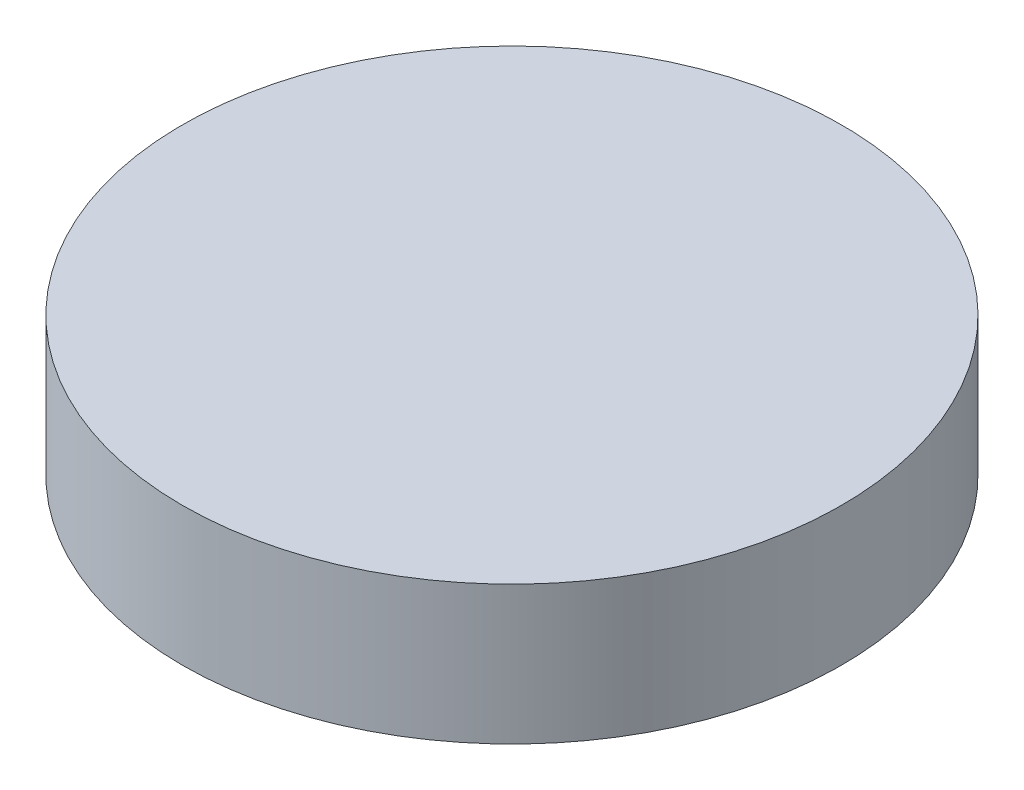
SolidWorks part; units mm, degrees
ref_plane "Front Plane" through (0, 0, 0) normal (0, 0, 1) x (1, 0, 0)
ref_plane "Top Plane" through (0, 0, 0) normal (0, 1, 0) x (1, 0, 0)
ref_plane "Right Plane" through (0, 0, 0) normal (1, 0, 0) x (0, 0, -1)
sketch "Sketch1" plane through (0, 0, 0) normal (0, 1, 0) x (1, 0, 0)
  circle A0 centre (0, 0) radius 7.5565
  dimension "D1" = 15.113
extrude "Boss-Extrude1" add sketch "Sketch1" along normal blind 3.175
